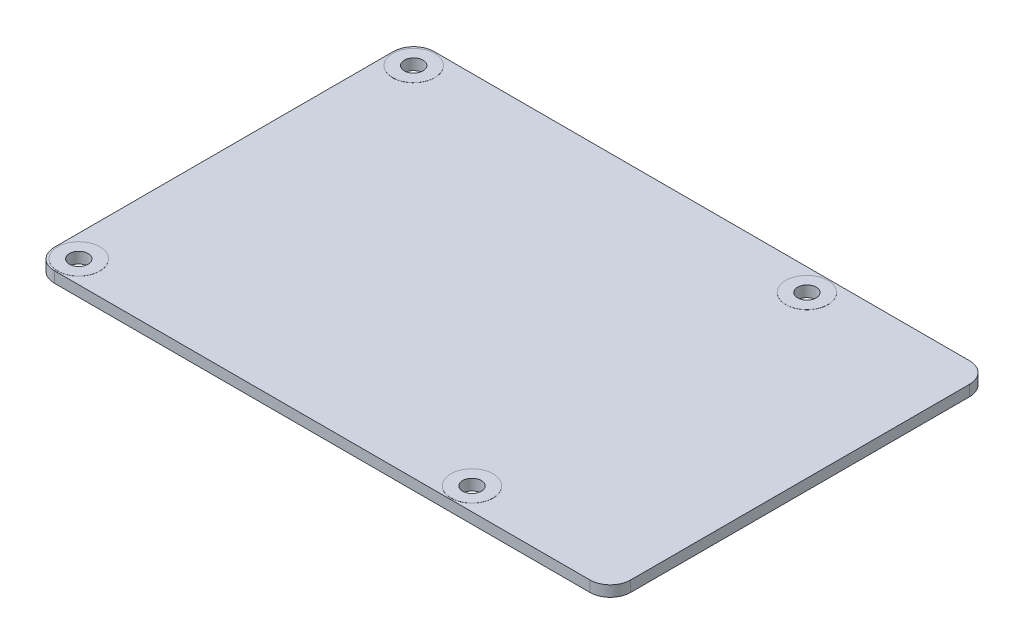
SolidWorks part; units mm, degrees
ref_plane "Front Plane" through (0, 0, 0) normal (0, 0, 1) x (1, 0, 0)
ref_plane "Top Plane" through (0, 0, 0) normal (0, 1, 0) x (1, 0, 0)
ref_plane "Right Plane" through (0, 0, 0) normal (1, 0, 0) x (0, 0, -1)
sketch "Sketch2" plane through (0, 0, 0) normal (0, 1, 0) x (1, 0, 0)
  line L0 (3.3, 52.7) -> (3.3, -4.2679) construction
  line L1 (3, 56) -> (82, 56)
  line L2 (0, 53) -> (0, 3)
  line L3 (3, 0) -> (82, 0)
  line L4 (85, 53) -> (85, 3)
  line L5 (3.3, 52.7) -> (61.3, 52.7) construction
  line L6 (61.3, 52.7) -> (61.3, 3.3) construction
  line L7 (61.3, 3.3) -> (3.3, 3.3) construction
  arc A0 (82, 0) -> (85, 3) centre (82, 3) ccw
  arc A1 (0, 3) -> (3, 0) centre (3, 3) ccw
  arc A2 (3, 56) -> (0, 53) centre (3, 53) ccw
  arc A3 (82, 56) -> (85, 53) centre (82, 53) cw
  circle A5 centre (3.3, 52.7) radius 3.1
  circle A6 centre (3.3, 3.3) radius 3.1
  circle A7 centre (61.3, 3.3) radius 3.1
  circle A8 centre (61.3, 52.7) radius 3.1
  point P8 (85, 0)
  point P11 (0, 0)
  point P14 (0, 56)
  point P17 (85, 56)
  dimension "D3" = 3
  dimension "D4" = 6.2
  dimension "D5" = 3
  dimension "D8" = 3.3
  dimension "D1" = 85
  dimension "D2" = 56
  dimension "D6" = 3.3
  dimension "D7" = 3.3
extrude "Boss-Extrude1" add sketch "Sketch2" along normal mid plane 1.6 contours L3 A0 L4 A3 L1 A2 L2 A1 | A8 | A7 | A6 | A5
sketch "Sketch3" plane through (0, 0, 0) normal (0, 1, 0) x (1, 0, 0)
  circle A0 centre (3.3, 3.3) radius 3.1
  circle A2 centre (61.3, 3.3) radius 3.1
  circle A3 centre (61.3, 52.7) radius 3.1
  circle A4 centre (3.3, 52.7) radius 3.1
  circle A5 centre (3.3, 52.7) radius 1.375
  circle A6 centre (61.3, 52.7) radius 1.375
  circle A7 centre (61.3, 3.3) radius 1.375
  circle A8 centre (3.3, 3.3) radius 1.375
extrude "Boss-Extrude3" add sketch "Sketch3" along normal mid plane 1.63
